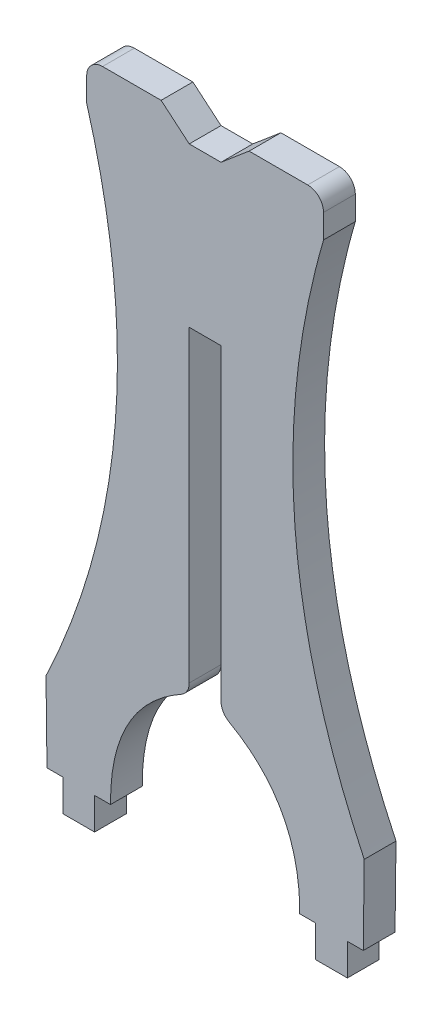
SolidWorks part; units mm, degrees
ref_plane "Front Plane" through (0, 0, 0) normal (0, 0, 1) x (1, 0, 0)
ref_plane "Top Plane" through (0, 0, 0) normal (0, 1, 0) x (1, 0, 0)
ref_plane "Right Plane" through (0, 0, 0) normal (1, 0, 0) x (0, 0, -1)
sketch "Sketch3" plane through (0, 0, 0) normal (0, 0, 1) x (1, 0, 0)
  line L17 (0.1483, -16.543) -> (-0.0059, -3.8439)
  line L47 (6.5002, 85.057) -> (6.5002, 78.707)
  line L57 (6.5002, 85.057) -> (18.4064, 85.057)
  line L67 (0.1483, -16.543) -> (2.6883, -16.543)
  line L71 (7.7683, -16.543) -> (10.3083, -16.543)
  line L74 (2.6883, -16.543) -> (2.6883, -21.623)
  line L75 (2.6883, -21.623) -> (7.7683, -21.623)
  line L76 (7.7683, -16.543) -> (7.7683, -21.623)
  line L105 (22.9031, 81.263) -> (18.4064, 85.057)
  line L113 (22.9031, 81.263) -> (27.9831, 81.263)
  line L116 (27.9831, 55.863) -> (22.9031, 55.863)
  line L118 (22.9031, 55.863) -> (22.9031, 5.063)
  line L121 (27.9831, 81.263) -> (32.4797, 85.057)
  line L122 (44.386, 85.057) -> (32.4797, 85.057)
  line L123 (44.386, 85.057) -> (44.386, 78.707)
  line L124 (50.7378, -16.543) -> (50.892, -3.8439)
  line L125 (50.7378, -16.543) -> (48.1978, -16.543)
  line L126 (48.1978, -16.543) -> (48.1978, -21.623)
  line L127 (48.1978, -21.623) -> (43.1178, -21.623)
  line L128 (43.1178, -16.543) -> (43.1178, -21.623)
  line L129 (43.1178, -16.543) -> (40.5778, -16.543)
  line L130 (27.9831, 55.863) -> (27.9831, 5.063)
  spline S0 degree 2 poles (6.5002, 78.707) (18.9018, 35.9899) (-0.0059, -3.8439) knots 0 0 0 1 1 1
  spline S1 degree 2 poles (22.9031, 5.063) (10.2023, -1.2212) (10.3083, -16.543) knots 0 0 0 1 1 1
  spline S2 degree 2 poles (44.386, 78.707) (31.9843, 35.9899) (50.892, -3.8439) knots 0 0 0 1 1 1
  spline S3 degree 2 poles (27.9831, 5.063) (40.6838, -1.2212) (40.5778, -16.543) knots 0 0 0 1 1 1
  dimension "D8" = 11.9062
  dimension "D2" = 6.35
  dimension "D4" = 10.16
  dimension "D7" = 12.7
  dimension "D10" = 5.08
  dimension "D11" = 5.08
extrude "Boss-Extrude2" add sketch "Sketch3" along normal blind 5.08
fillet "Fillet3" radius 2.54 2 edges at (6.5002, 85.057, 2.54) (44.386, 85.057, 2.54)
fillet "Fillet4" radius 2.54 2 edges at (27.9831, 5.063, 2.54) (22.9031, 5.063, 2.54)
